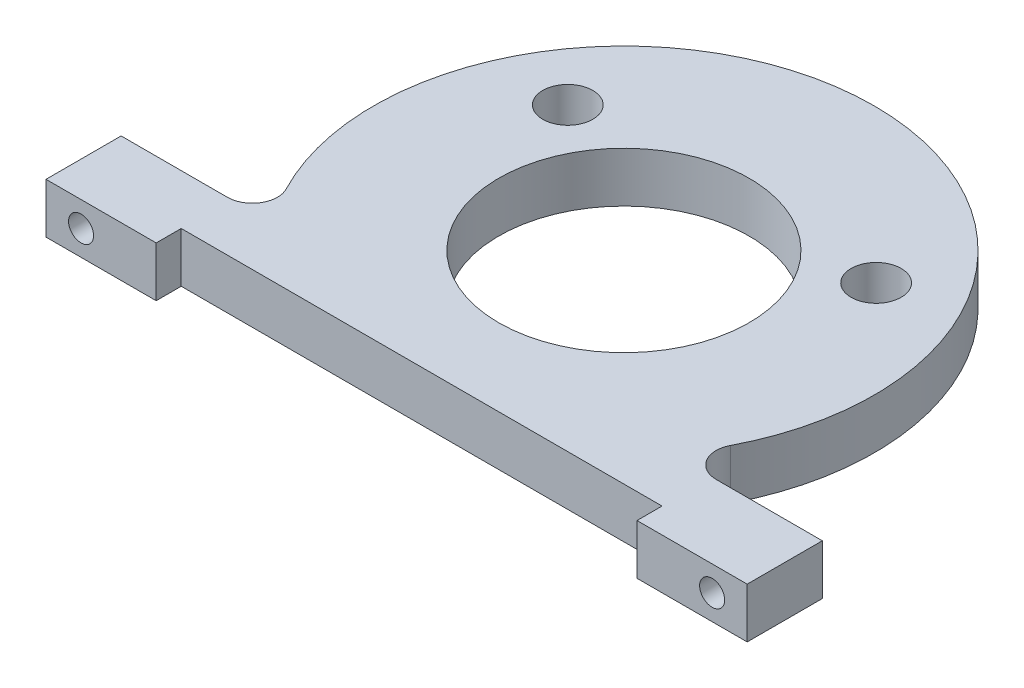
SolidWorks part; units mm, degrees
ref_plane "Front Plane" through (0, 0, 0) normal (0, 0, 1) x (1, 0, 0)
ref_plane "Top Plane" through (0, 0, 0) normal (0, 1, 0) x (1, 0, 0)
ref_plane "Right Plane" through (0, 0, 0) normal (1, 0, 0) x (0, 0, -1)
sketch "Sketch1" plane through (0, 0, 0) normal (0, 1, 0) x (1, 0, 0)
  line L0 (-99.0282, 0) -> (111.9621, 0) construction
  line L1 (0, 93.9763) -> (0, -96.5506) construction
  line L2 (-70, -30.3876) -> (-39.7063, -30.3876)
  line L3 (-70, -30.3876) -> (-70, -45.3876)
  line L4 (-70, -45.3876) -> (-48, -45.3876)
  line L5 (70, -30.3876) -> (70, -45.3876)
  line L6 (70, -45.3876) -> (48, -45.3876)
  line L7 (-48, -45.3876) -> (-48, -40.3876)
  line L8 (-48, -40.3876) -> (48, -40.3876)
  line L9 (48, -40.3876) -> (48, -45.3876)
  line L10 (39.7063, -30.3876) -> (70, -30.3876)
  line L12 (15.5536, 19.5726) -> (46.0099, 19.5726) construction
  line L13 (-46.0099, 19.5726) -> (-15.5536, 19.5726) construction
  arc A0 (39.7063, -30.3876) -> (-39.7063, -30.3876) centre (0, 0) ccw
  circle A1 centre (0, 0) radius 25
  circle A2 centre (30.7817, 19.5726) radius 5
  circle A3 centre (-30.7817, 19.5726) radius 5
  point P11 (0, -30.3876)
  dimension "D1" = 90
  dimension "D8" = 10
  dimension "D9" = 10
  dimension "D2" = 140
  dimension "D3" = 15
  dimension "D4" = 22
  dimension "D5" = 22
  dimension "D6" = 5
  dimension "D7" = 15
extrude "Boss-Extrude1" add sketch "Sketch1" along normal blind 10
sketch "Sketch3" plane through (0, 0, 30.3876) normal (0, 0, -1) x (-1, 0, 0)
  line L0 (-70, 5) -> (-56, 5) construction
  line L1 (-70, 10) -> (-70, 0) construction
  circle A0 centre (-63, 5) radius 2.5
  dimension "D2" = 5
  dimension "D1" = 14
extrude "Cut-Extrude1" cut sketch "Sketch3" against normal through all
cosmetic thread "Cosmetic Thread1" parameters "D2"=6
sketch "Sketch4" plane through (0, 0, 30.3876) normal (0, 0, -1) x (-1, 0, 0)
  line L0 (70, 5) -> (56, 5) construction
  line L1 (70, 10) -> (70, 0) construction
  circle A0 centre (63, 5) radius 2.5
  dimension "D2" = 5
  dimension "D1" = 14
extrude "Cut-Extrude2" cut sketch "Sketch4" against normal through all
cosmetic thread "Cosmetic Thread2" parameters "D2"=6
fillet "Fillet1" radius 5 1 edges at (39.7063, 5, 30.3876)
fillet "Fillet2" radius 5 1 edges at (-39.7063, 5, 30.3876)
